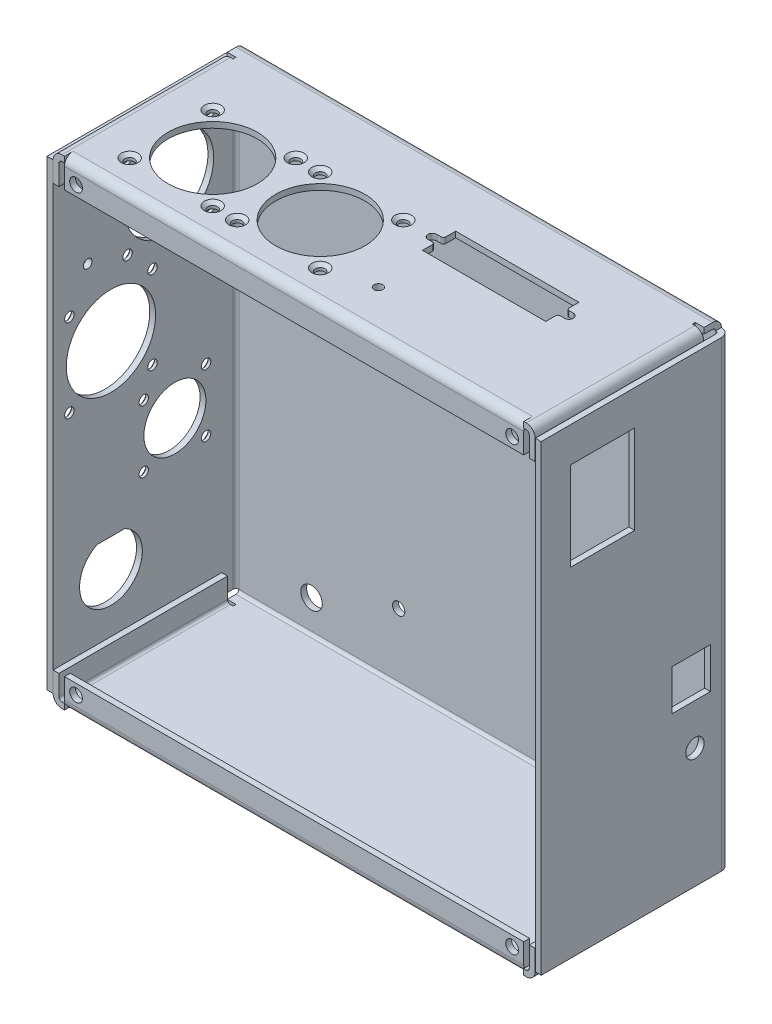
SolidWorks part; units mm, degrees
ref_plane "Front Plane" through (0, 0, 0) normal (0, 0, 1) x (1, 0, 0)
ref_plane "Top Plane" through (0, 0, 0) normal (0, 1, 0) x (1, 0, 0)
ref_plane "Right Plane" through (0, 0, 0) normal (1, 0, 0) x (0, 0, -1)
sketch "Sketch1" plane through (0, 0, 0) normal (1, 0, 0) x (0, 0, -1)
  line L0 (0, 79.5) -> (0, -79.5)
  dimension "D1" = 159
extrude "Extrude-Thin1" add sketch "Sketch1" along normal mid plane 164 thin
sketch "Sketch16" plane through (0, 0, 0) normal (1, 0, 0) x (0, 0, -1)
  line L0 (-2, -79.5) -> (-2, 79.5) construction
  line L1 (0, -79.5) -> (0, 79.5) construction
  line L2 (-3, 80.5) -> (-62, 80.5)
  line L3 (-63, 79.5) -> (-63, 72.5)
  line L4 (-3, 82.5) -> (-62, 82.5)
  line L5 (-65, 72.5) -> (-65, 79.5)
  line L6 (-2, 79.5) -> (0, 79.5) construction
  line L7 (-2, 79.5) -> (0, 79.5)
  line L8 (-63, 72.5) -> (-65, 72.5)
  arc A0 (-2, 79.5) -> (-3, 80.5) centre (-3, 79.5) ccw
  arc A1 (0, 79.5) -> (-3, 82.5) centre (-3, 79.5) ccw
  arc A2 (-62, 80.5) -> (-63, 79.5) centre (-62, 79.5) ccw
  arc A3 (-62, 82.5) -> (-65, 79.5) centre (-62, 79.5) ccw
  dimension "D1" = 3
  dimension "D2" = 65
  dimension "D3" = 10
extrude "Boss-Extrude3" add sketch "Sketch16" along normal mid plane 164
mirror "Mirror1" about plane through (0, 0, 0) normal (0, 1, 0) of "Boss-Extrude3"
sketch "Sketch18" plane through (0, 0, 0) normal (0, 1, 0) x (1, 0, 0)
  line L0 (82, 0) -> (-82, 0) construction
  line L1 (-85, -3) -> (-85, -65)
  line L2 (-85, -65) -> (-83, -65)
  line L3 (-83, -65) -> (-83, -3)
  line L4 (82, -65) -> (-82, -65) construction
  line L5 (-82, 0) -> (-82, -3) construction
  line L6 (-82, -3) -> (-82, -62) construction
  line L7 (-82, 0) -> (-82, -2)
  arc A0 (-82, 0) -> (-85, -3) centre (-82, -3) ccw
  arc A1 (-82, -2) -> (-83, -3) centre (-82, -3) ccw
  dimension "D2" = 2
extrude "Boss-Extrude4" add sketch "Sketch18" along normal mid plane 159
mirror "Mirror2" about plane through (0, 0, 0) normal (1, 0, 0) of "Boss-Extrude4"
sketch "Sketch19" plane through (0, 0, 2) normal (0, 0, 1) x (1, 0, 0)
  line L2 (-82, 82.5) -> (-82, 79.5) construction
  line L3 (-82.6671, 64.4675) -> (-79, 64.4675)
  line L4 (-82.6671, 64.4675) -> (-82.6671, 89.2912)
  line L5 (-82.6671, 89.2912) -> (-79, 89.2912)
  line L6 (-79, 64.4675) -> (-79, 89.2912)
  dimension "D1" = 3
extrude "Cut-Extrude1" cut sketch "Sketch19" along normal through all from offset 4
sketch "Sketch20" plane through (0, 0, 6) normal (0, 0, 1) x (1, 0, 0)
  line L0 (-79, 80.5) -> (-79, 82.5) construction
  line L1 (-82, 80.5) -> (-79, 80.5) construction
  line L2 (-79, 82.5) -> (-82, 82.5) construction
  line L3 (-79, 80.5) -> (-79, 82.5)
  line L4 (-79.9, 80.5) -> (-79, 80.5)
  line L5 (-79, 82.5) -> (-79.9, 82.5)
  line L6 (-83, 79.5) -> (-83, -79.5) construction
  line L8 (-82.9, 79.5) -> (-82.9, 72.5)
  line L9 (-82.9, 72.5) -> (-80.9, 72.5)
  line L10 (-80.9, 79.5) -> (-80.9, 72.5)
  arc A0 (-79.9, 80.5) -> (-80.9, 79.5) centre (-79.9, 79.5) ccw
  arc A1 (-79.9, 82.5) -> (-82.9, 79.5) centre (-79.9, 79.5) ccw
  dimension "D4" = 2
  dimension "D1" = 0.1
  dimension "D2" = 2
  dimension "D3" = 7
extrude "Boss-Extrude5" add sketch "Sketch20" along normal up to surface (58 mm away) from offset 1 up to face at (-84, 0, 65)
mirror "Mirror3" about plane through (0, 0, 0) normal (1, 0, 0) of "Boss-Extrude5", "Cut-Extrude1"
mirror "Mirror4" about plane through (0, 0, 0) normal (0, 1, 0) of "Mirror3", "Boss-Extrude5", "Cut-Extrude1"
sketch "Sketch21" plane through (0, 0, 2) normal (0, 0, 1) x (1, 0, 0)
  line L0 (-85, 79.5) -> (-85, -79.5) construction
  line L1 (79, 82.5) -> (-79, 82.5) construction
  line L2 (79, -82.5) -> (-79, -82.5) construction
  line L3 (85, 79.5) -> (85, -79.5) construction
  circle A0 centre (-27.02, 37.5) radius 2.11
  circle A1 centre (-27.02, -57.75) radius 2.11
  circle A2 centre (69.5, 37.5) radius 2.11
  circle A3 centre (69.5, -57.75) radius 2.11
  circle A4 centre (-57, 69.5) radius 3.695
  circle A5 centre (-57, -69.5) radius 3.695
  circle A6 centre (57, -69.5) radius 3.695
  circle A7 centre (57, 69.5) radius 3.695
  dimension "D3" = 4.22
  dimension "D6" = 7.39
  dimension "D1" = 96.52
  dimension "D2" = 95.25
  dimension "D4" = 15.5
  dimension "D5" = 45
  dimension "D7" = 28
  dimension "D8" = 28
  dimension "D9" = 13
  dimension "D10" = 13
extrude "Cut-Extrude2" cut sketch "Sketch21" against normal through all
sketch "Sketch22" plane through (-85, 0, 0) normal (-1, 0, 0) x (0, 0, 1)
  line L0 (40.2513, -42.8) -> (49.7487, -42.8)
  line L1 (39.6055, -32.79) -> (4.7574, -32.79) construction
  line L2 (65, 79.5) -> (65, -79.5) construction
  line L4 (65, 82.5) -> (7, 82.5) construction
  line L5 (65, -82.5) -> (7, -82.5) construction
  line L8 (12.28, -7.78) -> (33.72, -29.22) construction
  line L9 (0, -79.5) -> (0, 79.5) construction
  line L15 (39.2875, 66.7875) -> (10.7125, 38.2125) construction
  line L16 (30.7125, 29.7875) -> (59.2875, 1.2125) construction
  arc A0 (40.2513, -42.8) -> (49.7487, -42.8) centre (45, -52.5) ccw
  circle A1 centre (23, -18.5) radius 10.668
  circle A2 centre (12.28, -7.78) radius 1.25
  circle A3 centre (33.72, -7.78) radius 1.25
  circle A4 centre (33.72, -29.22) radius 1.25
  circle A5 centre (12.28, -29.22) radius 1.25
  circle A6 centre (25, 52.5) radius 15.367
  circle A7 centre (45, 15.5) radius 15.367
  circle A8 centre (10.7125, 66.7875) radius 1
  circle A9 centre (10.7125, 38.2125) radius 1
  circle A10 centre (30.7125, 29.7875) radius 1
  circle A11 centre (30.7125, 1.2125) radius 1
  circle A12 centre (59.2875, 1.2125) radius 1
  circle A13 centre (59.2875, 29.7875) radius 1
  circle A14 centre (39.2875, 38.2125) radius 1
  circle A15 centre (39.2875, 66.7875) radius 1
  circle A16 centre (45, -52.5) radius 14.5 construction
  circle A17 centre (53, 42.5) radius 1.5
  dimension "D5" = 10.8
  dimension "D8" = 21.336
  dimension "D9" = 2.5
  dimension "D15" = 30.734
  dimension "D19" = 2
  dimension "D12" = 29
  dimension "D16" = 3
  dimension "D3" = 34
  dimension "D4" = 9.7
  dimension "D6" = 21.44
  dimension "D7" = 21.44
  dimension "D10" = 23
  dimension "D11" = 30
  dimension "D13" = 37
  dimension "D14" = 25
  dimension "D17" = 28.575
  dimension "D18" = 28.575
  dimension "D20" = 28.575
  dimension "D21" = 28.575
  dimension "D22" = 12
  dimension "D23" = 30
  dimension "D24" = 14.29
  dimension "D25" = 45
  dimension "D26" = 40
  dimension "D27" = 45
extrude "Cut-Extrude3" cut sketch "Sketch22" against normal blind 3
sketch "Sketch23" plane through (0, 82.5, 0) normal (0, 1, 0) x (1, 0, 0)
  line L0 (0, 0) -> (0, -65) construction
  line L1 (10.6, -20) -> (53, -20)
  line L2 (10.6, -20) -> (10.6, -23.3782)
  line L3 (10.6, -31.43) -> (53, -31.43)
  line L4 (53, -20) -> (53, -23.3782)
  line L5 (82, 0) -> (-82, 0) construction
  line L6 (79, -65) -> (-79, -65) construction
  line L7 (8.3, -24.191) -> (9.7872, -24.191)
  line L8 (85, -3) -> (85, -65) construction
  line L9 (55.3, -27.239) -> (53.8128, -27.239)
  line L10 (53.8128, -24.191) -> (55.3, -24.191)
  line L11 (9.7872, -27.239) -> (8.3, -27.239)
  line L12 (10.6, -28.0518) -> (10.6, -31.43)
  line L13 (53, -28.0518) -> (53, -31.43)
  line L14 (-67.2875, -25.7125) -> (-38.7125, -54.2875) construction
  line L15 (-30.2875, -54.2875) -> (-1.7125, -25.7125) construction
  line L16 (-85, -3) -> (-85, -65) construction
  arc A0 (8.3, -24.191) -> (8.3, -27.239) centre (8.3, -25.715) ccw
  arc A1 (55.3, -27.239) -> (55.3, -24.191) centre (55.3, -25.715) ccw
  arc A2 (53.8128, -24.191) -> (53, -23.3782) centre (53.8128, -23.3782) cw
  arc A3 (53.8128, -27.239) -> (53, -28.0518) centre (53.8128, -28.0518) ccw
  arc A4 (9.7872, -27.239) -> (10.6, -28.0518) centre (9.7872, -28.0518) cw
  arc A5 (9.7872, -24.191) -> (10.6, -23.3782) centre (9.7872, -23.3782) ccw
  circle A6 centre (-53, -40) radius 15.367
  circle A7 centre (-16, -40) radius 15.367
  circle A8 centre (-30.2875, -25.7125) radius 1
  circle A9 centre (-1.7125, -25.7125) radius 1
  circle A10 centre (-1.7125, -54.2875) radius 1
  circle A11 centre (-30.2875, -54.2875) radius 1
  circle A12 centre (-38.7125, -54.2875) radius 1
  circle A13 centre (-38.7125, -25.7125) radius 1
  circle A14 centre (-67.2875, -25.7125) radius 1
  circle A15 centre (-67.2875, -54.2875) radius 1
  circle A16 centre (14, -50) radius 1.5
  point P26 (53, -27.239)
  point P29 (10.6, -27.239)
  dimension "D5" = 0.8128
  dimension "D8" = 30.734
  dimension "D9" = 2
  dimension "D16" = 3
  dimension "D1" = 42.4
  dimension "D2" = 11.43
  dimension "D3" = 32
  dimension "D4" = 20
  dimension "D6" = 47
  dimension "D7" = 3.048
  dimension "D10" = 32
  dimension "D11" = 37
  dimension "D12" = 40
  dimension "D13" = 28.575
  dimension "D14" = 28.575
  dimension "D15" = 28.575
  dimension "D17" = 30
  dimension "D18" = 10
extrude "Cut-Extrude4" cut sketch "Sketch23" against normal blind 3
hole_wizard "CSK for #4 Flat Head Machine Screw (100)1" positions "Sketch25" profile "Sketch24" countersink size "#4" standard "Ansi Inch"
sketch "Sketch25" plane through (-85, 0, 0) normal (-1, 0, 0) x (0, 0, 1)
  point P0 (12.28, -7.78)
  point P1 (33.72, -7.78)
  point P4 (33.72, -29.22)
  point P7 (12.28, -29.22)
  point P13 (10.7125, 66.7875)
  point P16 (39.2875, 66.7875)
  point P19 (39.2875, 38.2125)
  point P22 (59.2875, 29.7875)
  point P25 (59.2875, 1.2125)
  point P28 (30.7125, 1.2125)
  point P31 (30.7125, 29.7875)
  point P34 (10.7125, 38.2125)
sketch "Sketch24" plane through (-85, -7.78, 12.28) normal (0, 1, 0) x (0, 0, 1)
  line L0 (0, 0) -> (0, 10.9806)
  line L1 (0, 10.9806) -> (1.6319, 10)
  line L2 (1.6319, 10) -> (1.6319, 1.0284)
  line L3 (1.6319, 1.0284) -> (2.8575, 0)
  line L5 (2.8575, 0) -> (0, 0)
  line L6 (-1.6319, 1.0284) -> (-2.8575, 0) construction
  line L10 (0, 10.9806) -> (-1.632, 10) construction
  line L11 (0, -6.35) -> (0, 107.95) construction
  dimension "Hole Dia." = 3.2639
  dimension "Hole Depth" = 10
  dimension "Near C'Sink Dia." = 5.715
  dimension "Near C'Sink Angle" = 100
  dimension "Drill Angle" = 118
sketch "Sketch26" plane through (0, 0, 65) normal (0, 0, 1) x (1, 0, 0)
  line L0 (-75, -76) -> (75, 76) construction
  line L1 (79, 72.5) -> (-79, 72.5) construction
  line L2 (-79, 72.5) -> (-79, 79.5) construction
  circle A0 centre (-75, 76) radius 2.195
  circle A1 centre (75, 76) radius 2.195
  circle A2 centre (75, -76) radius 2.195
  circle A3 centre (-75, -76) radius 2.195
  dimension "D5" = 4.39
  dimension "D1" = 152
  dimension "D2" = 150
  dimension "D3" = 3.5
  dimension "D4" = 4
extrude "Cut-Extrude5" cut sketch "Sketch26" against normal blind 10
sketch "Sketch27" plane through (85, 0, 0) normal (1, 0, 0) x (0, 0, -1)
  line L0 (-65, 82.5) -> (-7, 82.5) construction
  line L1 (-55, 67.5) -> (-32.85, 67.5)
  line L2 (-55, 67.5) -> (-55, 37)
  line L3 (-55, 37) -> (-32.85, 37)
  line L4 (-32.85, 67.5) -> (-32.85, 37)
  line L5 (-65, 79.5) -> (-65, -79.5) construction
  line L10 (-19.081, -23.08) -> (-7.778, -23.08) construction
  line L11 (-20.081, -10.08) -> (-6.778, -10.08)
  line L12 (-20.081, -10.08) -> (-20.081, -24.08)
  line L13 (-20.081, -24.08) -> (-6.778, -24.08)
  line L14 (-6.778, -10.08) -> (-6.778, -24.08)
  line L15 (-7.778, -23.08) -> (-7.778, -11.08) construction
  line L16 (-19.081, -11.08) -> (-7.778, -11.08) construction
  line L17 (-19.081, -23.08) -> (-19.081, -11.08) construction
  circle A0 centre (-12.096, -38.26) radius 3.175
  dimension "D4" = 6.35
  dimension "D1" = 22.15
  dimension "D2" = 30.5
  dimension "D3" = 15
  dimension "D5" = 1
  dimension "D6" = 1
  dimension "D7" = 1
  dimension "D8" = 1
  dimension "D9" = 10
extrude "Cut-Extrude6" cut sketch "Sketch27" against normal blind 10
hole_wizard "CSK for #4 Flat Head Machine Screw (100)2" positions "Sketch29" profile "Sketch28" countersink size "#4" standard "Ansi Inch"
sketch "Sketch29" plane through (0, 82.5, 0) normal (0, 1, 0) x (-1, 0, 0)
  point P0 (67.2875, 25.7125)
  point P1 (38.7125, 25.7125)
  point P4 (30.2875, 25.7125)
  point P7 (1.7125, 25.7125)
  point P10 (1.7125, 54.2875)
  point P13 (30.2875, 54.2875)
  point P16 (38.7125, 54.2875)
  point P19 (67.2875, 54.2875)
sketch "Sketch28" plane through (-67.2875, 82.5, 25.7125) normal (1, 0, 0) x (0, 0, 1)
  line L0 (0, 0) -> (0, 10.9806)
  line L1 (0, 10.9806) -> (1.6319, 10)
  line L2 (1.6319, 10) -> (1.6319, 1.0284)
  line L3 (1.6319, 1.0284) -> (2.8575, 0)
  line L5 (2.8575, 0) -> (0, 0)
  line L6 (-1.6319, 1.0284) -> (-2.8575, 0) construction
  line L10 (0, 10.9806) -> (-1.6319, 10) construction
  line L11 (0, -6.35) -> (0, 107.95) construction
  dimension "Hole Dia." = 3.2639
  dimension "Hole Depth" = 10
  dimension "Near C'Sink Dia." = 5.715
  dimension "Near C'Sink Angle" = 100
  dimension "Drill Angle" = 118
